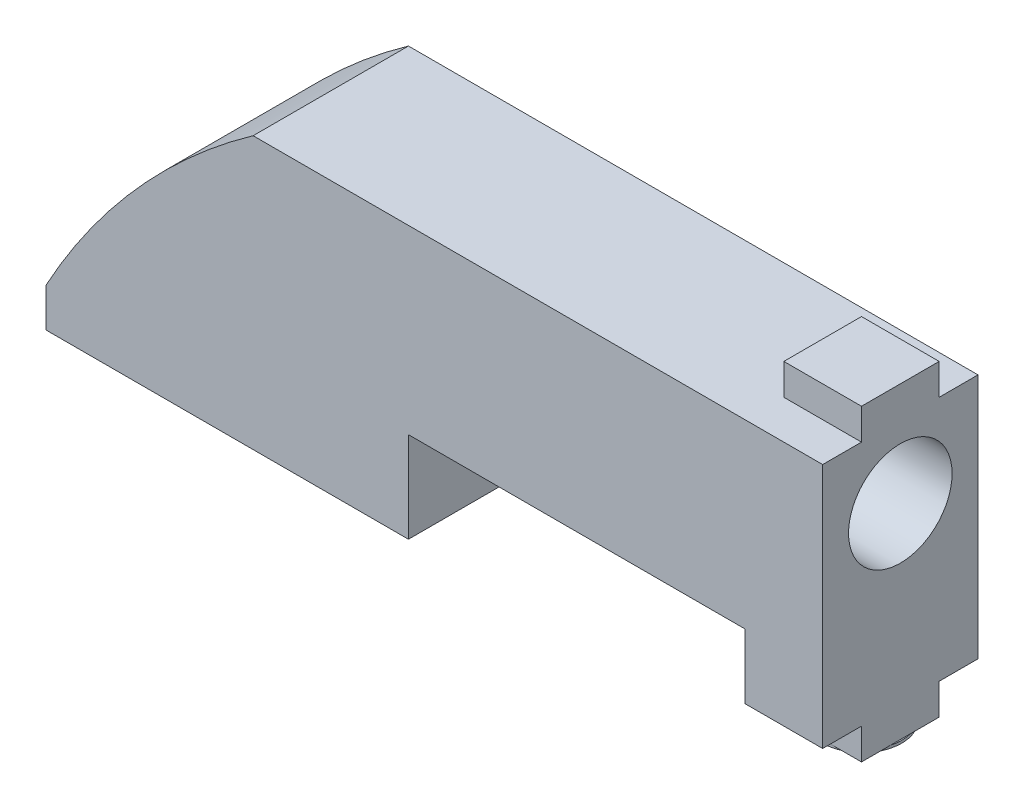
SolidWorks part; units mm, degrees
material "Alliage 7079"
ref_plane "Face" through (0, 0, 0) normal (0, 0, 1) x (1, 0, 0)
ref_plane "Dessus" through (0, 0, 0) normal (0, 1, 0) x (1, 0, 0)
ref_plane "Droite" through (0, 0, 0) normal (1, 0, 0) x (0, 0, -1)
sketch "Esquisse1" plane through (0, 0, 0) normal (0, 0, 1) x (1, 0, 0)
  line L0 (0, 0) -> (0, 1.5)
  line L2 (8, 10.5) -> (30, 10.5)
  line L3 (30, 10.5) -> (30, 1)
  line L4 (27, 1) -> (27, 3.5)
  line L5 (27, 3.5) -> (14, 3.5)
  line L6 (14, 3.5) -> (14, 0)
  line L7 (14, 0) -> (0, 0)
  line L9 (27, 1) -> (30, 1)
  arc A0 (8, 10.5) -> (0, 1.5) centre (23.3666, -11.2147) ccw
  dimension "D6" = 26.6019
  dimension "D1" = 9.5
  dimension "D2" = 10.5
  dimension "D3" = 1.5
  dimension "D4" = 13
  dimension "D5" = 7
  dimension "D7" = 22
  dimension "D8" = 8
  dimension "D9" = 14
extrude "Extrusion1" add sketch "Esquisse1" along normal mid plane 6
sketch "Esquisse2" plane through (0, 10.5, 0) normal (0, 1, 0) x (1, 0, 0)
  line L0 (30, -3) -> (30, 3) construction
  line L1 (30, 1.5) -> (27, 1.5)
  line L2 (30, 1.5) -> (30, -1.5)
  line L3 (30, -1.5) -> (27, -1.5)
  line L4 (27, 1.5) -> (27, -1.5)
  line L5 (31.5625, 0) -> (23.3666, 0) construction
  line L6 (23.3666, -3) -> (23.3666, 3) construction
  line L7 (30, 3) -> (8, 3) construction
  dimension "D1" = 3
  dimension "D2" = 3
  dimension "D3" = 3
extrude "Extrusion2" add sketch "Esquisse2" along normal blind 1.2
sketch "Esquisse3" plane through (0, 1, 0) normal (0, -1, 0) x (1, 0, 0)
  line L1 (27, 1.5) -> (30, 1.5)
  line L2 (27, 3) -> (27, -3) construction
  line L3 (27, -1.5) -> (30, -1.5)
  line L4 (30, 1.5) -> (30, -1.5)
  line L5 (30.8829, 0) -> (25.166, 0) construction
  line L6 (14, 3) -> (27, 3) construction
  line L7 (30, 3) -> (30, -3) construction
  line L8 (27, 1.5) -> (27, -1.5)
  dimension "D1" = 3
  dimension "D2" = 3
extrude "Extrusion3" add sketch "Esquisse3" along normal blind 1.2
hole_wizard "Diamètre du perçage Ø4.0 (4)1" positions "Esquisse5" profile "Esquisse4" hole size "Ø4.0" standard "ISO"
sketch "Esquisse5" plane through (30, 0, 0) normal (1, 0, 0) x (0, 0, -1)
  line L0 (-3, 1) -> (-3, 10.5) construction
  line L2 (1.5, 1) -> (3, 1) construction
  line L3 (1.5, 10.5) -> (3, 10.5) construction
  point P0 (0, 7.7)
  point P7 (2.25, 1)
  point P10 (2.25, 10.5)
  dimension "D1" = 3
  dimension "D2" = 6.7
  dimension "D3" = 2.8
sketch "Esquisse4" plane through (30, 7.7, 0) normal (0, 1, 0) x (0, 0, -1)
  line L0 (0, 0) -> (0, 4.2017)
  line L1 (0, 4.2017) -> (2, 3)
  line L2 (2, 3) -> (2, 0)
  line L5 (2, 0) -> (0, 0)
  line L10 (0, 4.2017) -> (-2, 3) construction
  line L11 (0, -6.35) -> (0, 107.95) construction
  dimension "Diamètre du perçage" = 4
  dimension "Profondeur du perçage" = 3
  dimension "Angle de pointe" = 118
sketch "Esquisse6" plane through (0, -0.2, 0) normal (0, -1, 0) x (1, 0, 0)
  circle A0 centre (28.5256, 0) radius 1.5256
extrude "Extrusion4" add sketch "Esquisse6" along normal blind 0.1
